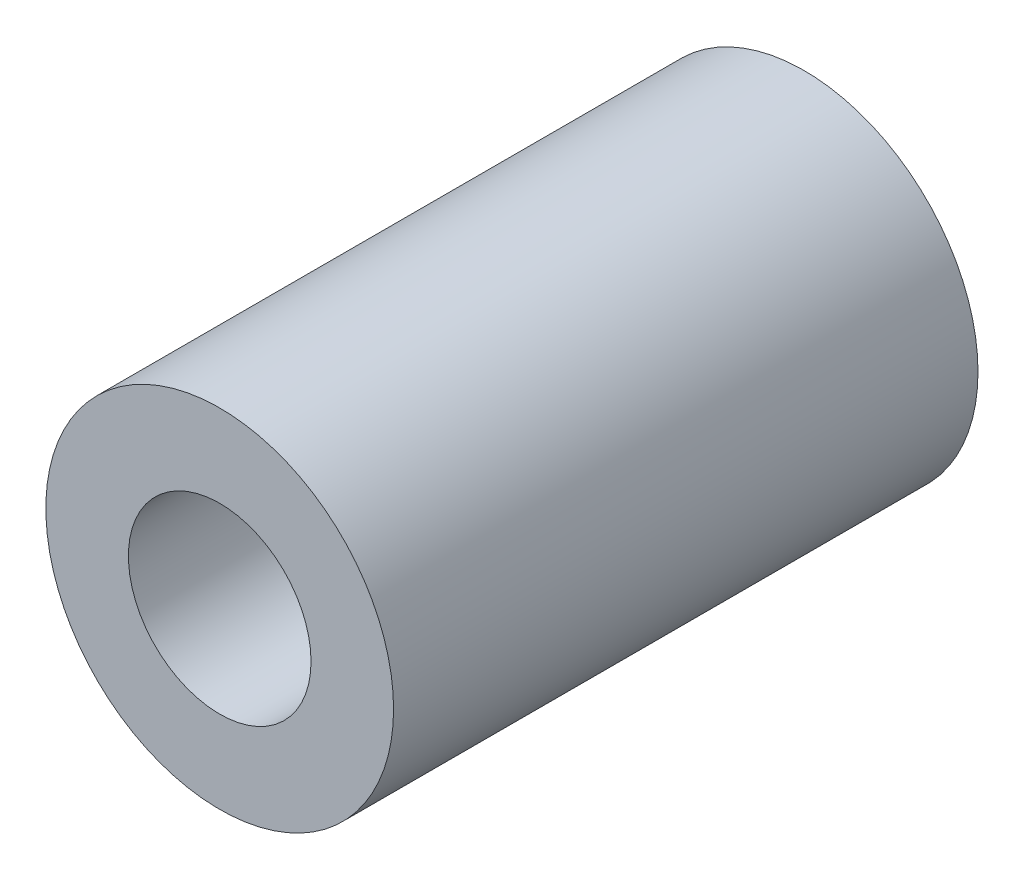
SolidWorks part; units mm, degrees
ref_plane "Front Plane" through (0, 0, 0) normal (0, 0, 1) x (1, 0, 0)
ref_plane "Top Plane" through (0, 0, 0) normal (0, 1, 0) x (1, 0, 0)
ref_plane "Right Plane" through (0, 0, 0) normal (1, 0, 0) x (0, 0, -1)
sketch "Sketch1" plane through (0, 0, 0) normal (0, 0, 1) x (1, 0, 0)
  circle A0 centre (0, 0) radius 1.25
  circle A1 centre (0, 0) radius 2.38
  dimension "D1" = 4.76
  dimension "D2" = 2.5
extrude "Boss-Extrude1" add sketch "Sketch1" along normal blind 8
